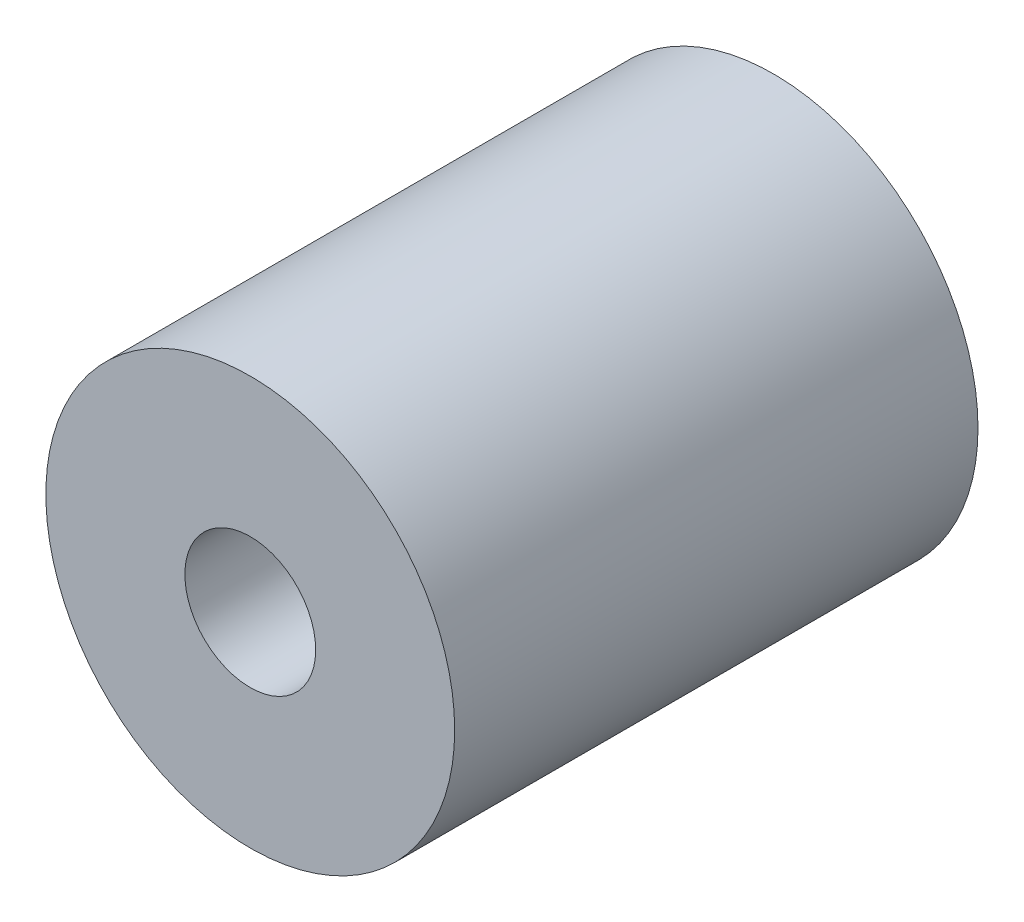
SolidWorks part; units mm, degrees
ref_plane "Plan1" through (0, 0, 0) normal (0, 0, 1) x (1, 0, 0)
ref_plane "Plan2" through (0, 0, 0) normal (0, 1, 0) x (1, 0, 0)
ref_plane "Plan3" through (0, 0, 0) normal (1, 0, 0) x (0, 0, -1)
sketch "Esquisse1" plane through (0, 0, 0) normal (0, 0, 1) x (1, 0, 0)
  circle A0 centre (0, 0) radius 12.5
  circle A1 centre (0, 0) radius 4
  dimension "D1" = 25
  dimension "D2" = 8
extrude "Base-Extrusion" add sketch "Esquisse1" along normal blind 32
